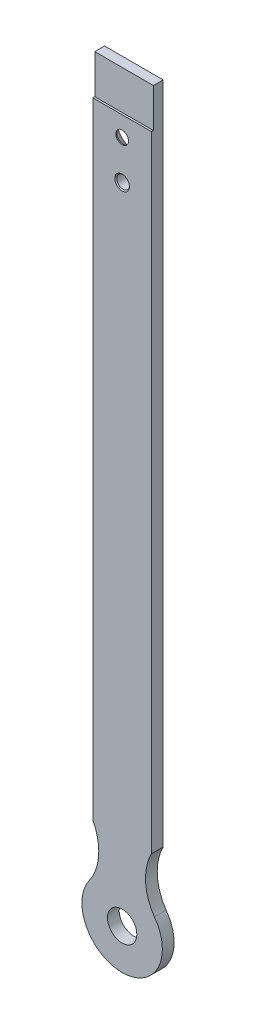
SolidWorks part; units mm, degrees
ref_plane "Спереди" through (0, 0, 0) normal (0, 0, 1) x (1, 0, 0)
ref_plane "Сверху" through (0, 0, 0) normal (0, 1, 0) x (1, 0, 0)
ref_plane "Справа" through (0, 0, 0) normal (1, 0, 0) x (0, 0, -1)
sketch "Эскиз1" plane through (0, 0, 0) normal (0, 0, 1) x (1, 0, 0)
  line L0 (15, 60.1262) -> (15, 400)
  line L1 (15, 400) -> (-15, 400)
  line L2 (0, 481.0809) -> (0, -73.6647) construction
  line L3 (-15, 60.1262) -> (-15, 400)
  arc A0 (-16.5121, 32.8596) -> (16.5121, 32.8596) centre (0, 20.5785) ccw
  arc A1 (16.5121, 32.8596) -> (15, 60.1262) centre (38.5826, 47.7588) cw
  arc A2 (-16.5121, 32.8596) -> (-15, 60.1262) centre (-38.5826, 47.7588) ccw
  circle A3 centre (0, 370) radius 3.25
  circle A4 centre (0, 350) radius 3.25
  circle A5 centre (0, 20.5785) radius 7.5
  point P13 (0, 400)
  point P15 (0, 0)
extrude "Бобышка-Вытянуть1" add sketch "Эскиз1" along normal blind 6
sketch "Эскиз2" plane through (-15, 0, 0) normal (-1, 0, 0) x (0, 0, 1)
  line L0 (5, 400) -> (5, 380.0564)
  line L1 (6, 400) -> (0, 400) construction
  line L2 (5, 380.0564) -> (6, 380.0564)
  line L3 (6, 400) -> (6, 60.1262) construction
  line L4 (6, 380.0564) -> (6, 400)
  line L5 (6, 400) -> (5, 400)
extrude "Вырез-Вытянуть1" cut sketch "Эскиз2" against normal through all
chamfer "Фаска1" distance 5.5 angle 45 1 edges at (3.25, 370, 0)
chamfer "Фаска2" distance 0.5 angle 45 2 edges at (3.25, 350, 0) (3.25, 350, 6)
